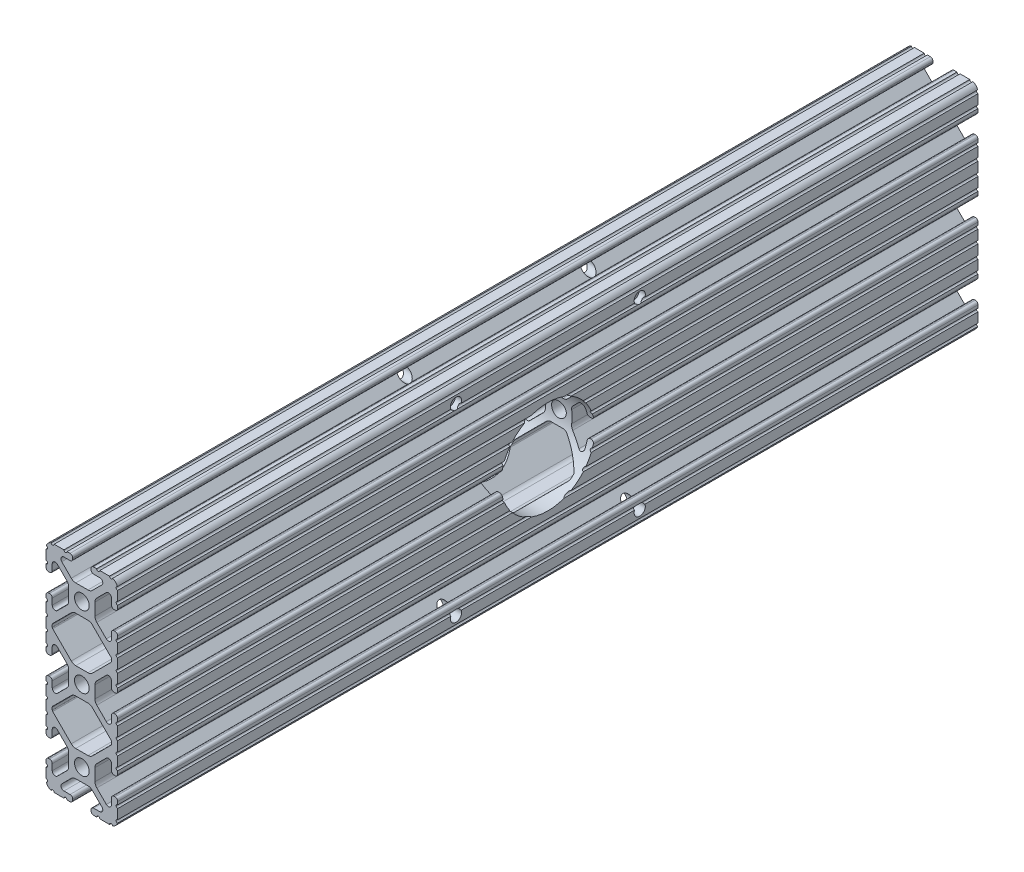
SolidWorks part; units mm, degrees
material "6061-T6 (SS)"
ref_plane "Front Plane" through (0, 0, 0) normal (0, 0, 1) x (1, 0, 0)
ref_plane "Top Plane" through (0, 0, 0) normal (0, 1, 0) x (1, 0, 0)
ref_plane "Right Plane" through (0, 0, 0) normal (1, 0, 0) x (0, 0, -1)
sketch "Sketch2" plane through (0, 0, 0) normal (0, 0, 1) x (1, 0, 0)
  line L0 (0, 38.1) -> (0, -38.1) construction
  line L1 (-12.7, 0) -> (12.7, 0) construction
  line L2 (3.2512, -38.1) -> (12.7, -38.1)
  line L3 (12.7, -38.1) -> (12.7, -28.6512)
  line L4 (3.2512, -38.1) -> (3.2512, -35.8902)
  line L5 (3.2512, -35.8902) -> (8.9276, -35.8902)
  line L6 (8.9276, -35.8902) -> (3.0856, -30.0482)
  line L7 (0, -25.4) -> (12.7, -38.1) construction
  line L8 (12.7, -28.6512) -> (10.4902, -28.6512)
  line L9 (10.4902, -28.6512) -> (10.4902, -34.3276)
  line L10 (10.4902, -34.3276) -> (4.6482, -28.4856)
  circle A0 centre (0, -25.4) radius 2.6035
  arc A1 (6.3485, -35.8902) -> (7.1039, -34.0665) centre (6.3485, -34.8219) ccw construction
  point P8 (0, -30.0482)
  dimension "Center Hole Diameter" = 5.207
  dimension "Rail Height" = 76.2
  dimension "Rail Width" = 25.4
  dimension "T-Slot Width" = 6.5024
  dimension "Slot Inner Width" = 14.8336
  dimension "Thickness" = 2.2098
  dimension "Slot Depth" = 5.842
  dimension "D1" = 2.2098
  dimension "D2" = 50.8
sketch "Sketch3" plane through (0, 0, 0) normal (1, 0, 0) x (0, 0, -1)
  line L0 (-152.4, -38.1) -> (152.4, -38.1) construction
  line L1 (-127, 0) -> (127, 0) construction
  dimension "D1" = 25.4
  dimension "Length" = 304.8
sketch "Sketch4" plane through (0, 0, 0) normal (0, 0, 1) x (1, 0, 0)
  line L0 (4.1904, -38.1) -> (10.1173, -38.1)
  line L1 (3.2512, -38.1) -> (12.7, -38.1) construction
  line L2 (3.2512, -38.1) -> (3.2512, -35.8902) construction
  line L3 (3.2512, -35.8902) -> (8.9276, -35.8902) construction
  line L4 (3.2512, -36.8294) -> (3.2512, -37.1608)
  line L5 (4.1904, -35.8902) -> (6.3485, -35.8902)
  line L6 (0, -30.0482) -> (2.164, -30.0482)
  line L7 (8.9276, -35.8902) -> (3.0856, -30.0482) construction
  line L8 (3.7373, -30.6999) -> (7.1039, -34.0665)
  line L9 (12.7, -38.1) -> (12.7, -28.6512) construction
  line L10 (10.4902, -34.3276) -> (4.6482, -28.4856) construction
  line L11 (10.4902, -28.6512) -> (10.4902, -34.3276) construction
  line L12 (10.4902, -31.7485) -> (10.4902, -29.5904)
  line L13 (12.7, -28.6512) -> (10.4902, -28.6512) construction
  line L14 (11.4294, -28.6512) -> (11.7608, -28.6512)
  line L15 (12.7, -29.5904) -> (12.7, -35.5173)
  line L16 (8.6665, -32.5039) -> (5.2999, -29.1373)
  line L17 (4.6482, -25.4) -> (4.6482, -27.564)
  line L19 (0, -30.0482) -> (0, -28.0035)
  line L20 (0, 38.1) -> (0, -38.1) construction
  line L21 (4.6482, -25.4) -> (2.6035, -25.4)
  arc A0 (3.2512, -37.1608) -> (4.1904, -38.1) centre (4.1904, -37.1608) ccw
  circle A1 centre (0, -25.4) radius 2.6035 construction
  arc A2 (3.2512, -36.8294) -> (4.1904, -35.8902) centre (4.1904, -36.8294) cw
  arc A3 (6.3485, -35.8902) -> (7.1039, -34.0665) centre (6.3485, -34.8219) ccw
  arc A4 (2.164, -30.0482) -> (3.7373, -30.6999) centre (2.164, -32.2732) cw
  arc A5 (10.1173, -38.1) -> (12.7, -35.5173) centre (10.1173, -35.5173) ccw
  arc A6 (8.6665, -32.5039) -> (10.4902, -31.7485) centre (9.4219, -31.7485) ccw
  arc A7 (10.4902, -29.5904) -> (11.4294, -28.6512) centre (11.4294, -29.5904) cw
  arc A8 (11.7608, -28.6512) -> (12.7, -29.5904) centre (11.7608, -29.5904) cw
  arc A9 (5.2999, -29.1373) -> (4.6482, -27.564) centre (6.8732, -27.564) cw
  arc A11 (0, -28.0035) -> (2.6035, -25.4) centre (0, -25.4) ccw
  dimension "D1" = 2.5827
  dimension "D2" = 2.225
  dimension "D3" = 0.9392
extrude "Boss-Extrude1" add sketch "Sketch4" along normal mid plane 304.8
sketch "Sketch5" plane through (0, 0, 0) normal (0, 0, 1) x (1, 0, 0)
  line L0 (3.2512, -38.1) -> (12.7, -38.1) construction
  line L1 (4.1904, -35.8902) -> (6.3485, -35.8902) construction
  line L3 (0, -25.4) -> (12.7, -38.1) construction
  line L4 (6.3485, -35.8902) -> (6.3485, -38.1) construction
  line L5 (8.9276, -35.8902) -> (3.0856, -30.0482) construction
  circle A0 centre (10.3562, -38.1) radius 0.5524
  circle A1 centre (5.796, -38.1) radius 0.5524
  circle A2 centre (12.7, -35.7562) radius 0.5525
  circle A3 centre (12.7, -31.196) radius 0.5525
  point P10 (5.2694, -35.8902)
  point P12 (9.4219, -31.7485)
  dimension "D1" = 1.1049
extrude "Cut-Extrude1" cut sketch "Sketch5" against normal through all both and the other way through all
mirror "Mirror1" about plane through (4.6482, -25.4, 152.4) normal (0, -1, 0) of bodies 137 134
sketch "Sketch6" plane through (0, 0, 0) normal (0, 0, 1) x (1, 0, 0)
  line L0 (12.7, -14.4914) -> (12.7, -12.7)
  line L1 (12.7, -12.7) -> (9.8037, -12.7)
  line L3 (9.8037, -12.7) -> (9.8037, -15.5963)
  line L4 (9.8037, -15.5963) -> (12.7, -15.5963)
  line L5 (6.3485, -12.7) -> (9.8037, -12.7) construction
  circle A0 centre (12.7, -15.0438) radius 0.5525 construction
  arc A1 (12.7, -14.4914) -> (12.7, -15.5963) centre (12.7, -15.0438) ccw
  arc A4 (9.8037, -12.7) -> (10.8954, -12.82) centre (10.3562, -12.7) ccw construction
extrude "Boss-Extrude2" add sketch "Sketch6" along normal mid plane 304.8
sketch "Sketch7" plane through (0, 0, 0) normal (0, 0, 1) x (1, 0, 0)
  line L0 (5.4206, -18.4168) -> (10.3284, -13.509)
  line L1 (3.7373, -20.1001) -> (7.1039, -16.7335) construction
  line L2 (10.4902, -13.1184) -> (10.4902, -12.7)
  line L3 (0, -12.7) -> (10.4902, -12.7)
  line L5 (0, -12.7) -> (5.4206, -18.4168)
  line L7 (0, 38.1) -> (0, -38.1) construction
  line L8 (6.3485, -12.7) -> (12.7, -12.7) construction
  arc A0 (10.3284, -13.509) -> (10.4902, -13.1184) centre (9.9377, -13.1184) ccw
  circle A3 centre (12.7, -15.0438) radius 0.5525 construction
extrude "Cut-Extrude2" cut sketch "Sketch7" against normal through all both and the other way through all
mirror "Mirror2" about plane through (4.1904, -12.7, 152.4) normal (0, -1, 0) of bodies 139 135
other "SurfaceCut1"
mirror "Mirror3" about plane through (0, 0, 0) normal (1, 0, 0) of bodies 142 136
mirror "Mirror4" about plane through (0, 0, 0) normal (0, 1, 0) of bodies 140
sketch "Sketch8" plane through (-12.7, 0, 0) normal (-1, 0, 0) x (0, 0, 1)
  line L1 (32.5501, 32.5501) -> (-32.5501, 32.5501) construction
  line L2 (32.5501, 32.5501) -> (32.5501, -32.5501) construction
  line L3 (32.5501, -32.5501) -> (-32.5501, -32.5501) construction
  line L4 (-32.5501, 32.5501) -> (-32.5501, -32.5501) construction
  line L5 (32.5501, 32.5501) -> (-32.5501, -32.5501) construction
  line L6 (32.5501, -32.5501) -> (-32.5501, 32.5501) construction
  circle A0 centre (-32.5501, 32.5501) radius 1.9812
  circle A1 centre (32.5501, 32.5501) radius 1.9812
  circle A2 centre (32.5501, -32.5501) radius 1.9812
  circle A3 centre (-32.5501, -32.5501) radius 1.9812
  circle A4 centre (0, 0) radius 16.637
  point P0 (0, 0)
  dimension "D1" = 3.9624
  dimension "D3" = 33.274
  dimension "D2" = 65.1002
extrude "Cut-Extrude3" cut sketch "Sketch8" against normal through all
equation "\"D1@Boss-Extrude1\"= \"altitude_vertictal_rail_length\""
equation "\"D1@Sketch2\"=\"Thickness@Sketch2\""
equation "\"D2@Sketch4\"=\"Slot Inner Width@Sketch2\"*0.15"
equation "\"D1@Sketch4\"=\"D3@Sketch4\"*2.75"
equation "\"D3@Sketch4\"=\"Thickness@Sketch2\"*0.425"
equation "\"D1@Sketch5\"= \"Thickness@Sketch2\" * 0.5"
equation "\"D1@Boss-Extrude2\"= \"altitude_vertictal_rail_length\""
equation "\"azimuth_horizontal_rail_length\"=(\"altitude_horizontal_rail_length\"+6in-0.29in)"
equation "\"azimuth_vertictal_rail_length\"=6in"
equation "\"wall_screw_clearance_diameter\"=4.3mm"
equation "\"altitude_horizontal_rail_length\"=10in"
equation "\"altitude_vertictal_rail_length\"=12in"
